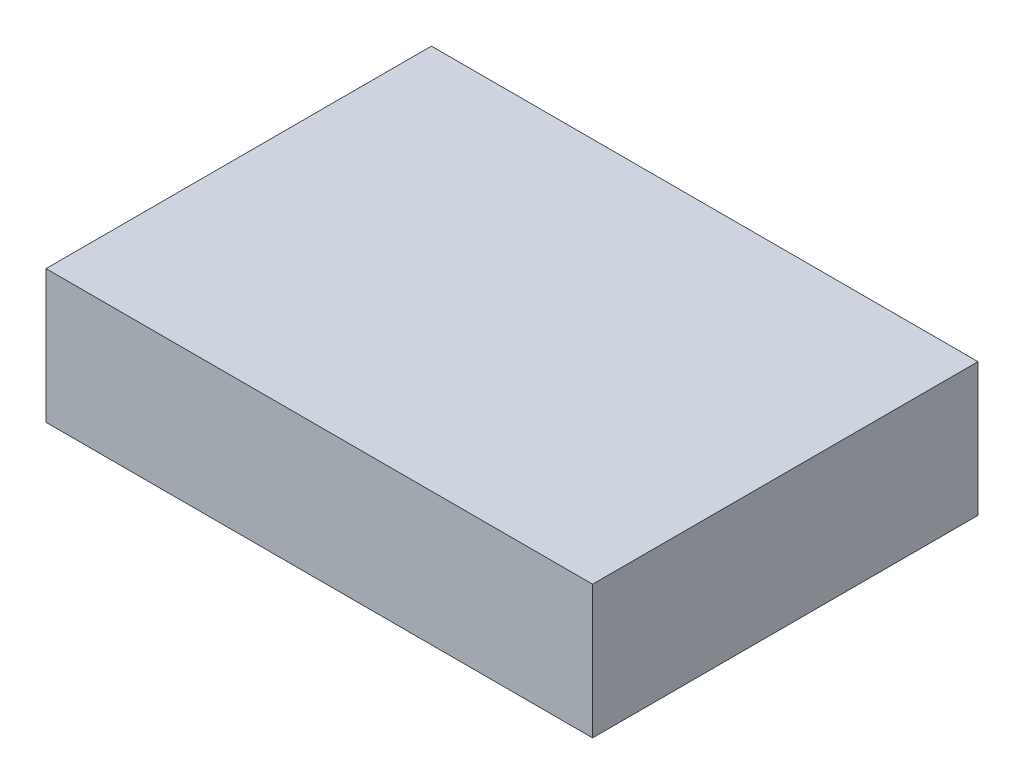
SolidWorks part; units mm, degrees
ref_plane "Front Plane" through (0, 0, 0) normal (0, 0, 1) x (1, 0, 0)
ref_plane "Top Plane" through (0, 0, 0) normal (0, 1, 0) x (1, 0, 0)
ref_plane "Right Plane" through (0, 0, 0) normal (1, 0, 0) x (0, 0, -1)
sketch "Sketch1" plane through (0, 0, 0) normal (0, 1, 0) x (1, 0, 0)
  line L1 (0, 0) -> (-78, 0)
  line L2 (0, 0) -> (0, -55)
  line L3 (0, -55) -> (-78, -55)
  line L4 (-78, 0) -> (-78, -55)
  dimension "D1" = 78
  dimension "D2" = 55
extrude "Boss-Extrude1" add sketch "Sketch1" along normal blind 19
